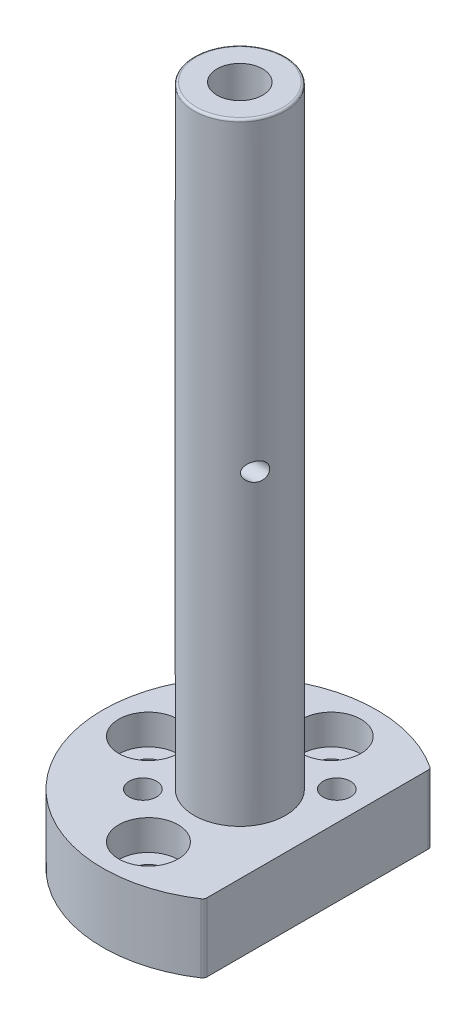
SolidWorks part; units mm, degrees
material "3003 Alloy"
ref_plane "Front Plane" through (0, 0, 0) normal (0, 0, 1) x (1, 0, 0)
ref_plane "Top Plane" through (0, 0, 0) normal (0, 1, 0) x (1, 0, 0)
ref_plane "Right Plane" through (0, 0, 0) normal (1, 0, 0) x (0, 0, -1)
sketch "Sketch1" plane through (0, 0, 0) normal (0, 1, 0) x (1, 0, 0)
  line L0 (0, 0) -> (0, 30) construction
  line L1 (17, -24.7184) -> (17, 24.7184)
  arc A0 (17, 24.7184) -> (17, -24.7184) centre (0, 0) ccw
  dimension "D1" = 60
  dimension "D2" = 17
extrude "Boss-Extrude1" add sketch "Sketch1" along normal blind 15
sketch "Sketch2" plane through (0, 15, 0) normal (0, 1, 0) x (1, 0, 0)
  circle A0 centre (0, 0) radius 10
  dimension "D1" = 20
extrude "Boss-Extrude2" add sketch "Sketch2" along normal blind 134
sketch "Sketch4" plane through (0, 0, 0) normal (0, -1, 0) x (1, 0, 0)
  circle A0 centre (0, 0) radius 7.25
  dimension "D1" = 14.5
extrude "Cut-Extrude1" cut sketch "Sketch4" against normal blind 57
sketch "Sketch5" plane through (0, 57, 0) normal (0, -1, 0) x (1, 0, 0)
  circle A1 centre (0, 0) radius 5
  dimension "D1" = 10
extrude "Cut-Extrude2" cut sketch "Sketch5" against normal through all
sketch "Sketch7" plane through (0, 15, 0) normal (0, 1, 0) x (1, 0, 0)
  line L0 (0, 0) -> (-30, 0) construction
  circle A0 centre (0, -20) radius 6.5
  circle A3 centre (-20, 0) radius 6.5
  circle A6 centre (0, 20) radius 6.5 [skipped]
  circle A7 centre (20, 0) radius 6.5 [skipped]
  circle A8 centre (0, 0) radius 30 construction
  circle A9 centre (0, 20) radius 6.5
  point P9 (0, 0)
  point P13 (0, 0)
  dimension "D2" = 13
  dimension "D1" = 20
  dimension "D3" = 4
extrude "Cut-Extrude3" cut sketch "Sketch7" against normal blind 6.6
sketch "Sketch8" plane through (0, 8.4, 0) normal (0, 1, 0) x (1, 0, 0)
  circle A0 centre (0, -20) radius 3.3
  circle A3 centre (-20, 0) radius 3.3
  circle A6 centre (0, 20) radius 3.3 [skipped]
  circle A7 centre (20, 0) radius 3.3 [skipped]
  circle A9 centre (0, 20) radius 3.3
  point P14 (0, 0)
  dimension "D1" = 6.6
  dimension "D2" = 4
  dimension "D4" = 20
extrude "Cut-Extrude4" cut sketch "Sketch8" against normal through all
sketch "Sketch9" plane through (0, 15, 0) normal (0, 1, 0) x (1, 0, 0)
  line L0 (0, 0) -> (-30, 0) construction
  line L1 (-10.6066, -10.6066) -> (0, 0) construction
  line L2 (0, 0) -> (10.6066, 10.6066) construction
  circle A0 centre (-10.6066, -10.6066) radius 3
  arc A1 (17, 24.7184) -> (17, -24.7184) centre (0, 0) ccw construction
  circle A2 centre (10.6066, 10.6066) radius 3
  dimension "D1" = 6
  dimension "D5" = 6
  dimension "D2" = 15
  dimension "D3" = 45
  dimension "D4" = 15
extrude "Cut-Extrude5" cut sketch "Sketch9" against normal through all
fillet "Fillet1" radius 1 2 edges at (17, 7.5, 24.7184) (17, 7.5, -24.7184)
fillet "Fillet2" radius 0.5 1 edges at (0, 149, 10)
sketch "Sketch10" plane through (17, 0, 0) normal (1, 0, 0) x (0, 0, -1)
  circle A0 centre (-5, 82) radius 2
  dimension "D3" = 4
  dimension "D1" = 5
  dimension "D2" = 82
extrude "Cut-Extrude11" cut sketch "Sketch10" against normal through all
